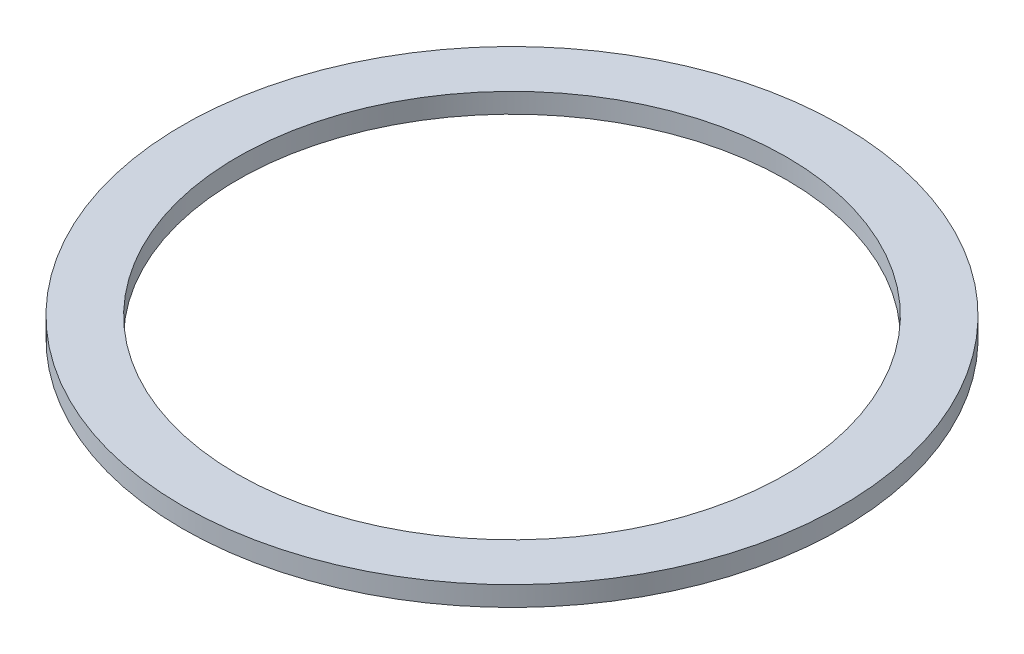
SolidWorks part; units mm, degrees
ref_plane "Alzado" through (0, 0, 0) normal (0, 0, 1) x (1, 0, 0)
ref_plane "Planta" through (0, 0, 0) normal (0, 1, 0) x (1, 0, 0)
ref_plane "Vista lateral" through (0, 0, 0) normal (1, 0, 0) x (0, 0, -1)
sketch "Croquis1" plane through (0, 0, 0) normal (0, 1, 0) x (1, 0, 0)
  line L0 (0, 0) -> (125, 0) construction
  line L1 (-150, 150) -> (150, 150) construction
  line L2 (-150, 150) -> (-150, -150) construction
  line L3 (-150, -150) -> (150, -150) construction
  line L4 (150, 150) -> (150, -150) construction
  line L5 (-150, 150) -> (150, -150) construction
  line L6 (-150, -150) -> (150, 150) construction
  circle A0 centre (0, 0) radius 150
  circle A1 centre (0, 0) radius 125
  point P0 (0, 0)
  dimension "D3" = 250
  dimension "D1" = 300
  dimension "D2" = 300
extrude "Saliente-Extruir1" add sketch "Croquis1" along normal blind 9
sketch "Croquis2" plane through (0, 0, 0) normal (0, 1, 0) x (1, 0, 0)
  line L0 (0, 0) -> (125, 0) construction
  line L1 (125, 25) -> (140, 25)
  line L2 (110, 20.9808) -> (110, -20.9808)
  line L3 (125, -25) -> (140, -25)
  line L4 (140, 25) -> (140, -25)
  line L5 (110, 25) -> (140, -25) construction
  line L6 (110, -25) -> (140, 25) construction
  line L7 (110, 20.9808) -> (125, 25)
  line L8 (110, -20.9808) -> (125, -25)
  line L9 (-31.8301, -97.0929) -> (-35.8494, -112.0929)
  line L10 (-35.8494, -112.0929) -> (-43.3494, -125.0833)
  line L11 (-43.3494, -125.0833) -> (-86.6506, -100.0833)
  line L12 (-79.1506, -87.0929) -> (-86.6506, -100.0833)
  line L13 (-68.1699, -76.1122) -> (-79.1506, -87.0929)
  line L14 (-31.8301, -97.0929) -> (-68.1699, -76.1122)
  line L15 (-63.1699, 84.7724) -> (-74.1506, 95.7532)
  line L16 (-74.1506, 95.7532) -> (-81.6506, 108.7436)
  line L17 (-81.6506, 108.7436) -> (-38.3494, 133.7436)
  line L18 (-30.8494, 120.7532) -> (-38.3494, 133.7436)
  line L19 (-26.8301, 105.7532) -> (-30.8494, 120.7532)
  line L20 (-63.1699, 84.7724) -> (-26.8301, 105.7532)
  circle A0 centre (0, 0) radius 125 construction
  point P0 (125, 0)
  point P29 (0, 0)
  point P30 (5, 2.8868)
  dimension "D1" = 50
  dimension "D2" = 30
  dimension "D3" = 15
  dimension "D4" = 15
  dimension "D5" = 15
  dimension "D6" = 15
  dimension "D7" = 3
extrude "Saliente-Extruir3" [suppressed] add sketch "Croquis2" along normal blind 9
